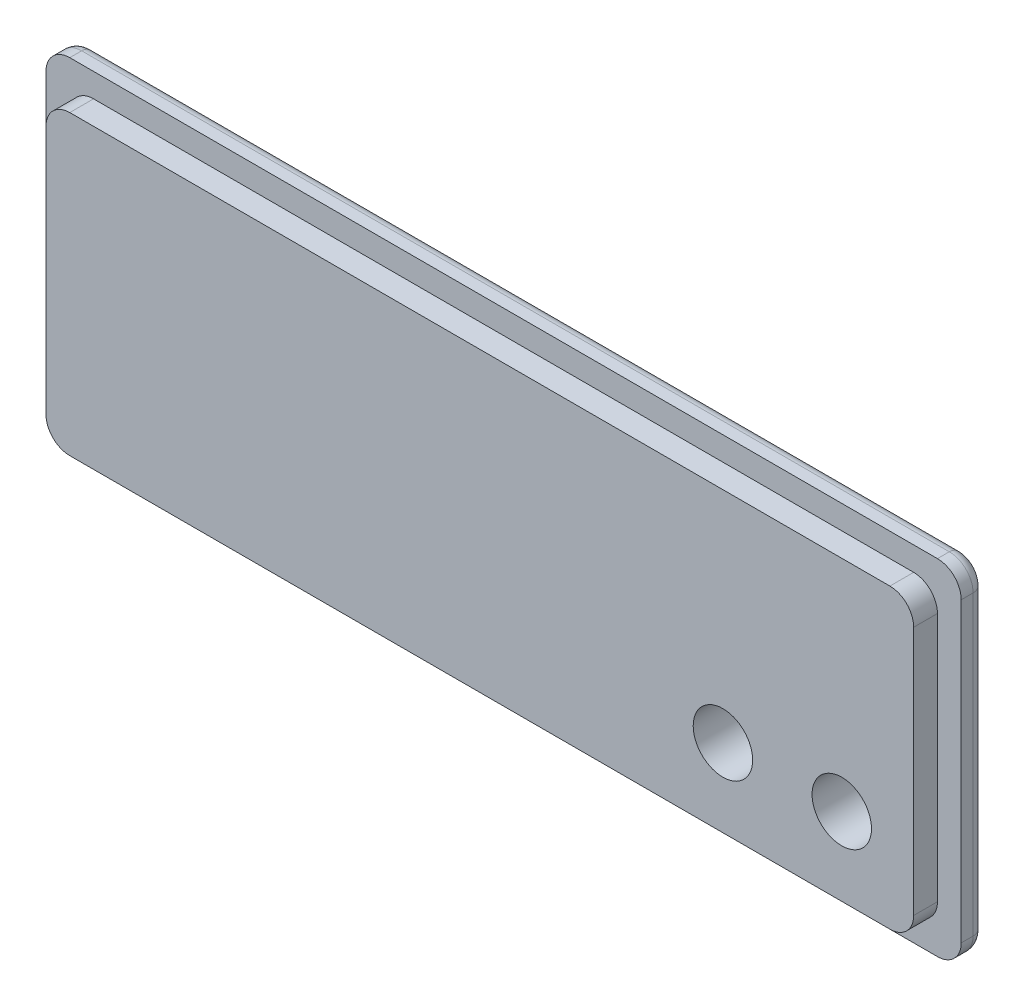
SolidWorks part; units mm, degrees
ref_plane "Front Plane" through (0, 0, 0) normal (0, 0, 1) x (1, 0, 0)
ref_plane "Top Plane" through (0, 0, 0) normal (0, 1, 0) x (1, 0, 0)
ref_plane "Right Plane" through (0, 0, 0) normal (1, 0, 0) x (0, 0, -1)
sketch "Sketch1" plane through (0, 0, 0) normal (0, 0, 1) x (1, 0, 0)
  line L1 (36.5, -14.5) -> (-36.5, -14.5)
  line L2 (38.5, -12.5) -> (38.5, 12.5)
  line L3 (36.5, 14.5) -> (-36.5, 14.5)
  line L4 (-38.5, -12.5) -> (-38.5, 12.5)
  line L5 (38.5, -14.5) -> (-38.5, 14.5) construction
  line L6 (38.5, 14.5) -> (-38.5, -14.5) construction
  arc A0 (36.5, -14.5) -> (38.5, -12.5) centre (36.5, -12.5) ccw
  arc A1 (38.5, 12.5) -> (36.5, 14.5) centre (36.5, 12.5) ccw
  arc A2 (-36.5, -14.5) -> (-38.5, -12.5) centre (-36.5, -12.5) cw
  arc A3 (-36.5, 14.5) -> (-38.5, 12.5) centre (-36.5, 12.5) ccw
  point P0 (0, 0)
  dimension "D1" = 2
extrude "Boss-Extrude1" add sketch "Sketch1" along normal blind 2
sketch "Sketch2" plane through (0, 0, 2) normal (0, 0, 1) x (1, 0, 0)
  line L1 (34.5, -12.5) -> (-34.5, -12.5)
  line L2 (36.5, -10.5) -> (36.5, 10.5)
  line L3 (34.5, 12.5) -> (-34.5, 12.5)
  line L4 (-36.5, -10.5) -> (-36.5, 10.5)
  line L5 (36.5, -12.5) -> (-36.5, 12.5) construction
  line L6 (36.5, 12.5) -> (-36.5, -12.5) construction
  arc A0 (34.5, -12.5) -> (36.5, -10.5) centre (34.5, -10.5) ccw
  arc A1 (36.5, 10.5) -> (34.5, 12.5) centre (34.5, 10.5) ccw
  arc A2 (-34.5, -12.5) -> (-36.5, -10.5) centre (-34.5, -10.5) cw
  arc A3 (-34.5, 12.5) -> (-36.5, 10.5) centre (-34.5, 10.5) ccw
  point P0 (0, 0)
  dimension "D1" = 2
extrude "Boss-Extrude2" add sketch "Sketch2" along normal blind 2
sketch "Sketch3" plane through (0, 0, 0) normal (0, 0, -1) x (-1, 0, 0)
  circle A0 centre (-30.4504, -5.9522) radius 2.5
  circle A1 centre (-20.4504, -5.9522) radius 2.5
extrude "Cut-Extrude1" cut sketch "Sketch3" against normal blind 10
fillet "Fillet1" radius 1 8 edges at (37.9142, 13.9142, 0) (38.5, 0, 0) (37.9142, -13.9142, 0) (0, -14.5, 0) (-37.9142, -13.9142, 0) (-38.5, 0, 0) (-37.9142, 13.9142, 0) (0, 14.5, 0)
